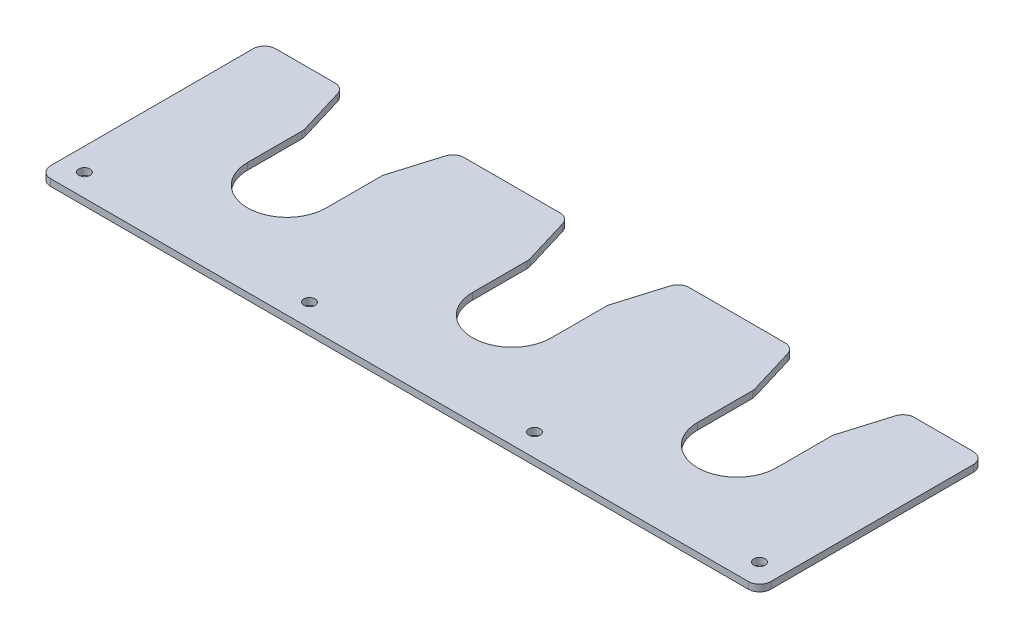
SolidWorks part; units mm, degrees
ref_plane "Front Plane" through (0, 0, 0) normal (0, 0, 1) x (1, 0, 0)
ref_plane "Top Plane" through (0, 0, 0) normal (0, 1, 0) x (1, 0, 0)
ref_plane "Right Plane" through (0, 0, 0) normal (1, 0, 0) x (0, 0, -1)
sketch "Sketch1" plane through (0, 0, 0) normal (0, 1, 0) x (1, 0, 0)
  line L1 (-160, 0) -> (160, 0)
  line L2 (-160, 0) -> (-160, 100)
  line L3 (-160, 100) -> (160, 100)
  line L4 (160, 0) -> (160, 100)
  point P4 (0, 0)
  dimension "D1" = 100
  dimension "D2" = 320
extrude "Boss-Extrude1" add sketch "Sketch1" along normal blind 3
sketch "Sketch2" plane through (0, 3, 0) normal (0, 1, 0) x (1, 0, 0)
  line L0 (-160, 100) -> (-160, 0) construction
  line L1 (-160, 0) -> (160, 0) construction
  circle A0 centre (-150, 10) radius 2.5
  dimension "D1" = 5
  dimension "D2" = 10
  dimension "D3" = 10
extrude "Cut-Extrude1" cut sketch "Sketch2" against normal through all
pattern_linear "LPattern1" count 4 spacing 100 along (1, 0, 0) of "Cut-Extrude1"
sketch "Sketch3" plane through (0, 3, 0) normal (0, 1, 0) x (1, 0, 0)
  line L0 (-125, 100) -> (-117.5, 75)
  line L1 (160, 100) -> (-160, 100) construction
  line L2 (-117.5, 75) -> (-117.5, 50)
  line L3 (-75, 100) -> (-82.5, 75)
  line L4 (-82.5, 75) -> (-82.5, 50)
  line L5 (-160, 0) -> (160, 0) construction
  line L6 (-100, 32.5) -> (-100, 100) construction
  line L7 (-125, 100) -> (-75, 100)
  arc A0 (-82.5, 50) -> (-117.5, 50) centre (-100, 50) cw
  circle A3 centre (-150, 10) radius 2.5 construction
  dimension "D1" = 35
  dimension "D2" = 50
  dimension "D3" = 50
  dimension "D4" = 50
  dimension "D5" = 25
extrude "Cut-Extrude2" cut sketch "Sketch3" against normal through all
fillet "Fillet1" radius 5 4 edges at (-75, 1.5, -100) (-82.5, 1.5, -75) (-117.5, 1.5, -75) (-125, 1.5, -100)
pattern_linear "LPattern2" count 3 spacing 100 along (1, 0, 0) of "Cut-Extrude2", "Fillet1"
fillet "Fillet2" radius 5 4 edges at (160, 1.5, 0) (160, 1.5, -100) (-160, 1.5, 0) (-160, 1.5, -100)
